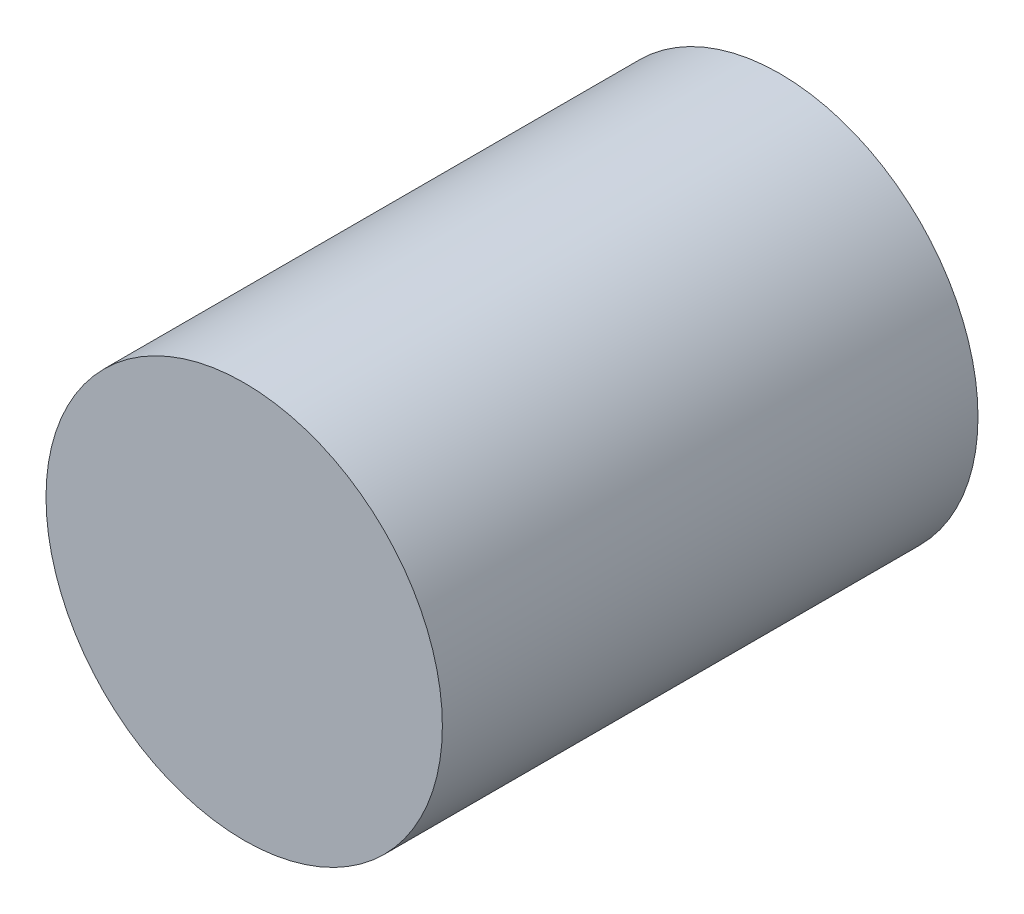
SolidWorks part; units mm, degrees
ref_plane "Front" through (0, 0, 0) normal (0, 0, 1) x (1, 0, 0)
ref_plane "Top" through (0, 0, 0) normal (0, 1, 0) x (1, 0, 0)
ref_plane "Right" through (0, 0, 0) normal (1, 0, 0) x (0, 0, -1)
sketch "Sketch1" plane through (0, 0, 0) normal (0, 0, 1) x (1, 0, 0)
  circle A0 centre (0, 0) radius 4.699
  dimension "D1" = 9.398
extrude "Base-Extrude" add sketch "Sketch1" along normal blind 12.7
scale "Scale1" [suppressed]
